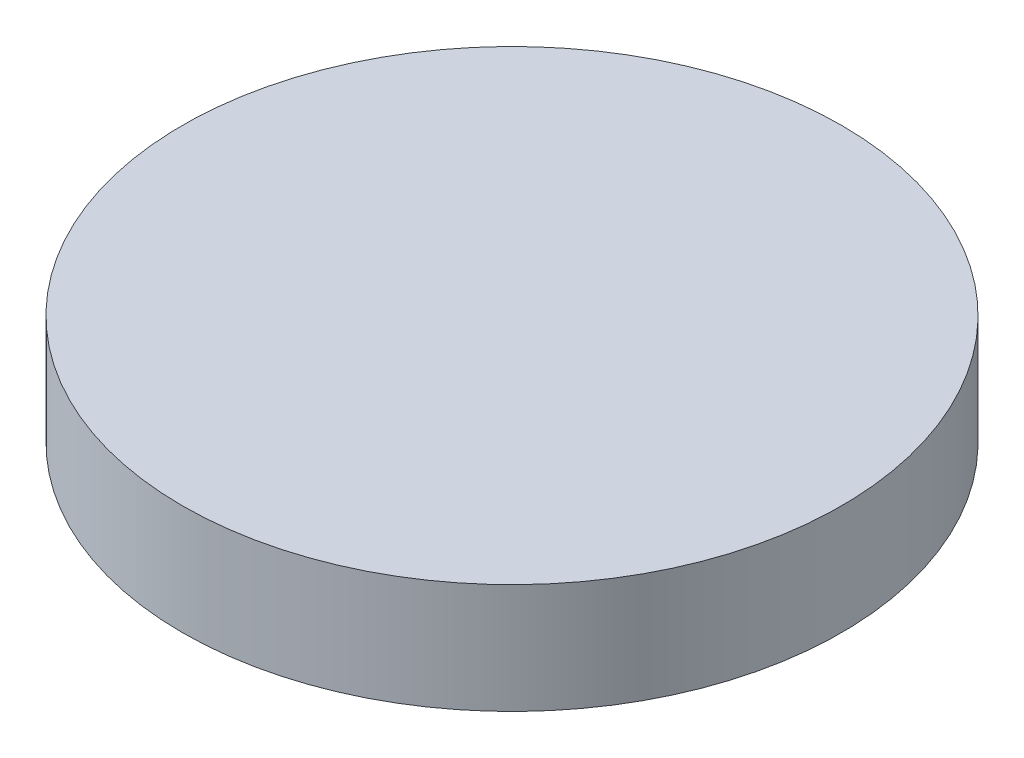
SolidWorks part; units mm, degrees
ref_plane "前视基准面" through (0, 0, 0) normal (0, 0, 1) x (1, 0, 0)
ref_plane "上视基准面" through (0, 0, 0) normal (0, 1, 0) x (1, 0, 0)
ref_plane "右视基准面" through (0, 0, 0) normal (1, 0, 0) x (0, 0, -1)
sketch "草图1" plane through (0, 0, 0) normal (0, 1, 0) x (1, 0, 0)
  circle A0 centre (0, 0) radius 76.2
  dimension "D1" = 152.4
extrude "凸台-拉伸1" add sketch "草图1" along normal blind 25.4
